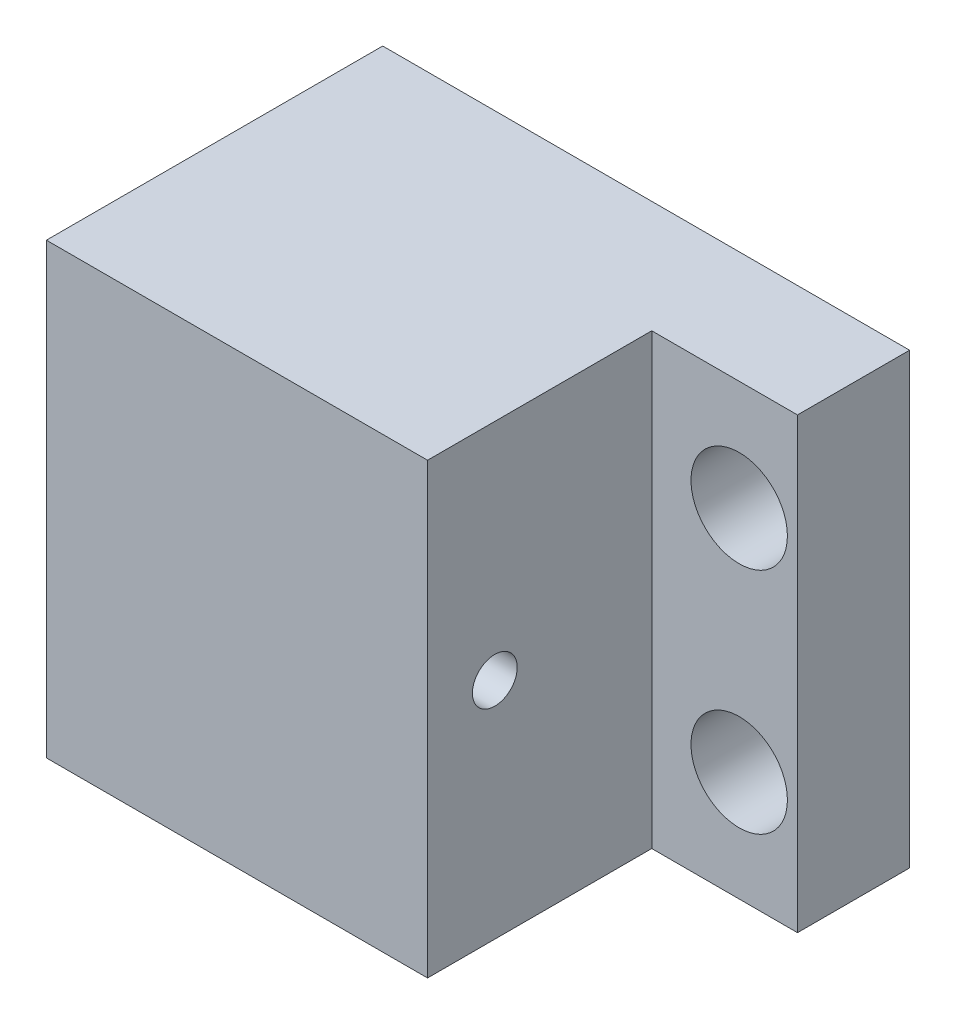
SolidWorks part; units mm, degrees
ref_plane "Front Plane" through (0, 0, 0) normal (0, 0, 1) x (1, 0, 0)
ref_plane "Top Plane" through (0, 0, 0) normal (0, 1, 0) x (1, 0, 0)
ref_plane "Right Plane" through (0, 0, 0) normal (1, 0, 0) x (0, 0, -1)
sketch "Sketch1" plane through (0, 0, 0) normal (0, 0, 1) x (1, 0, 0)
  line L0 (-12.1025, 7.8897) -> (11.3975, 7.8897)
  line L1 (-12.1025, 27.8897) -> (11.3975, 27.8897)
  line L2 (11.3975, 7.8897) -> (11.3975, 27.8897)
  line L3 (-12.1025, 27.8897) -> (-12.1025, 26.8897)
  line L4 (-12.1025, 8.8897) -> (-1.1025, 8.8897)
  line L5 (-1.1025, 8.8897) -> (-0.1025, 8.8897)
  line L6 (-0.1025, 8.8897) -> (-0.1025, 12.7906)
  line L7 (-0.1025, 12.7906) -> (1.8975, 12.7906)
  line L8 (1.8975, 12.7906) -> (1.8975, 22.9887)
  line L9 (1.8975, 22.9887) -> (-0.1025, 22.9887)
  line L10 (-0.1025, 22.9887) -> (-0.1025, 26.8897)
  line L11 (-0.1025, 26.8897) -> (-12.1025, 26.8897)
  line L12 (-12.1025, 7.8897) -> (-12.1025, 8.8897)
  dimension "D1" = 1.8975
  dimension "D2" = 11.3975
  dimension "D3" = 0.1025
  dimension "D4" = 1.1025
  dimension "D5" = 12.1025
  dimension "D6" = 7.8897
  dimension "D7" = 12.7906
  dimension "D8" = 22.9887
extrude "Boss-Extrude1" add sketch "Sketch1" along normal blind 5
sketch "Sketch2" plane through (0, 0, 5) normal (0, 0, 1) x (1, 0, 0)
  line L0 (-12.1025, 7.8897) -> (4.8975, 7.8897)
  line L1 (-12.1025, 7.8897) -> (-12.1025, 27.8897)
  line L2 (-12.1025, 27.8897) -> (4.8975, 27.8897)
  line L3 (4.8975, 7.8897) -> (4.8975, 27.8897)
  line L6 (-12.1025, 8.8897) -> (-12.1025, 7.8897) construction
  line L7 (11.3975, 27.8897) -> (-12.1025, 27.8897) construction
  dimension "D1" = 17
  dimension "D2" = 20
extrude "Boss-Extrude2" add sketch "Sketch2" along normal blind 10
sketch "Sketch3" plane through (4.8975, 0, 0) normal (1, 0, 0) x (0, 0, -1)
  line L0 (-5, 17.8897) -> (-15, 17.8897) construction
  line L1 (-15, 7.8897) -> (-15, 27.8897) construction
  line L2 (-5, 7.8897) -> (-5, 27.8897) construction
  circle A0 centre (-12, 17.8897) radius 1
  point P4 (0, 0)
  point P7 (0, 0)
  point P10 (0, 0)
  dimension "D1" = 2
  dimension "D2" = 7
extrude "Cut-Extrude1" cut sketch "Sketch3" against normal through all
sketch "Sketch4" plane through (0, 0, 5) normal (0, 0, 1) x (1, 0, 0)
  line L0 (-12.1025, 7.8897) -> (4.8975, 7.8897) construction
  line L1 (4.8975, 7.8897) -> (4.8975, 27.8897) construction
  circle A0 centre (8.7975, 12.7897) radius 2.15
  circle A1 centre (8.7975, 22.9897) radius 2.15
  dimension "D1" = 4.3
  dimension "D2" = 15.1
  dimension "D3" = 4.9
  dimension "D4" = 3.9
extrude "Cut-Extrude2" cut sketch "Sketch4" against normal through all
